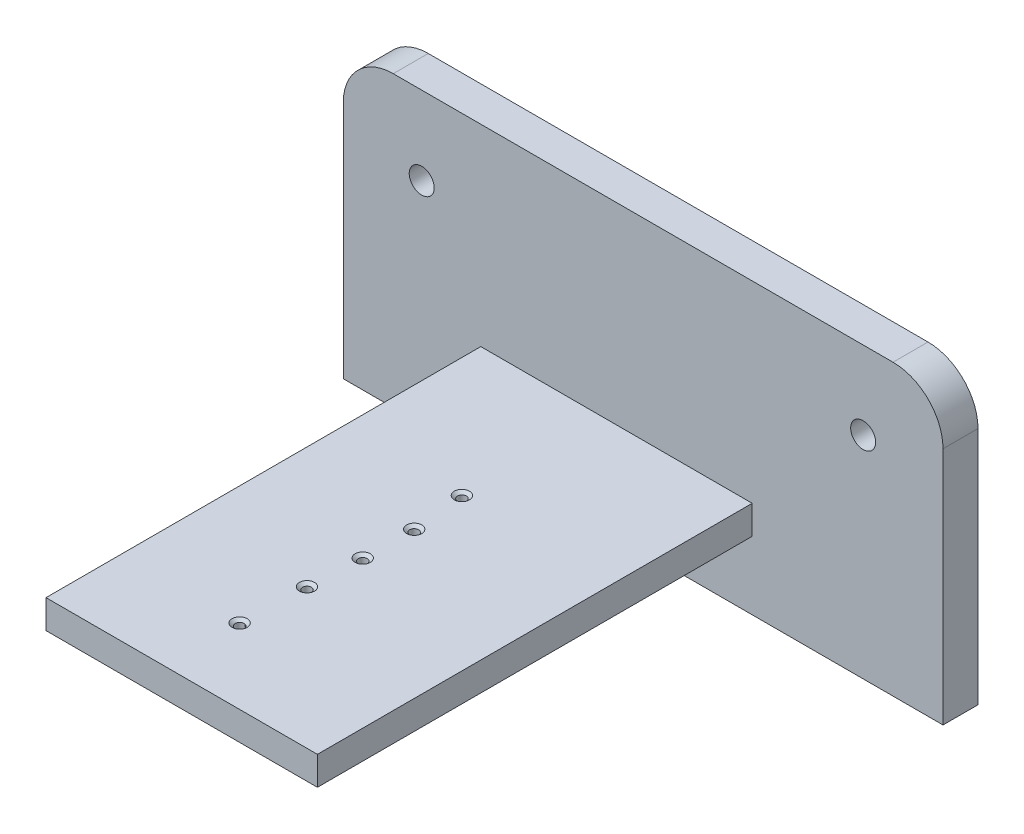
SolidWorks part; units mm, degrees
ref_plane "Front Plane" through (0, 0, 0) normal (0, 0, 1) x (1, 0, 0)
ref_plane "Top Plane" through (0, 0, 0) normal (0, 1, 0) x (1, 0, 0)
ref_plane "Right Plane" through (0, 0, 0) normal (1, 0, 0) x (0, 0, -1)
sketch "Sketch1" plane through (0, 0, 0) normal (0, 0, 1) x (1, 0, 0)
  line L1 (-60.1068, -28.7722) -> (59.8932, -28.7722)
  line L2 (-60.1068, -28.7722) -> (-60.1068, 29.0925)
  line L3 (-60.1068, 29.0925) -> (59.8932, 29.0925)
  line L4 (59.8932, -28.7722) -> (59.8932, 29.0925)
  line L5 (-60.1068, -28.7722) -> (59.8932, 29.0925) construction
  line L6 (-60.1068, 29.0925) -> (59.8932, -28.7722) construction
  line L7 (-60.2135, 13.6121) -> (59.573, 13.5053) construction
  circle A0 centre (-44.4128, 13.3986) radius 2.5
  circle A2 centre (43.913, 13.4684) radius 2.5
  point P0 (-0.1068, 0.1601)
  point P13 (0, 0)
  point P16 (42.4773, 12.7928)
  point P17 (40.5349, 13.7217)
  point P18 (43.913, 13.4684)
  dimension "D3" = 5
  dimension "D4" = 5
  dimension "D1" = 120
  dimension "D2" = 57.8648
extrude "Boss-Extrude1" add sketch "Sketch1" along normal blind 7
sketch "Sketch2" plane through (0, 0, 7) normal (0, 0, 1) x (1, 0, 0)
  line L1 (-32.5899, -15.1625) -> (21.7161, -15.1625)
  line L2 (-32.5899, -15.1625) -> (-32.5899, -9.4426)
  line L3 (-32.5899, -9.4426) -> (21.7161, -9.4426)
  line L4 (21.7161, -15.1625) -> (21.7161, -9.4426)
  line L5 (-32.5899, -15.1625) -> (21.7161, -9.4426) construction
  line L6 (-32.5899, -9.4426) -> (21.7161, -15.1625) construction
  point P0 (-5.4369, -12.3026)
extrude "Boss-Extrude2" add sketch "Sketch2" along normal blind 87
fillet "Fillet1" radius 10 2 edges at (59.8932, 29.0925, 3.5) (-60.1068, 29.0925, 3.5)
hole_wizard "CSK for #0 Flat Head Machine Screw (100)1" positions "Sketch3" profile "Sketch4" countersink size "#0" standard "ANSI Inch" end condition through all
sketch "Sketch3" plane through (0, -9.4426, 0) normal (0, 1, 0) x (1, 0, 0)
  point P0 (-8.6754, -34.6996)
  point P2 (-7.5993, -45.3149)
  point P4 (-7.7572, -55.463)
  point P6 (-8.364, -66.0078)
  point P8 (-8.8168, -79.0274)
sketch "Sketch4" plane through (-8.6754, -9.4426, 34.6996) normal (1, 0, 0) x (0, 0, 1)
  line L0 (0, 0) -> (0, 19.3296)
  line L1 (0, 19.3296) -> (0.889, 19.3296)
  line L2 (0.889, 19.3296) -> (0.889, 0.5222)
  line L3 (0.889, 0.5222) -> (1.5113, 0)
  line L5 (1.5113, 0) -> (0, 0)
  line L6 (-0.889, 0.5222) -> (-1.5113, 0) construction
  line L11 (0, -6.35) -> (0, 107.95) construction
  dimension "Thru Hole Dia." = 1.778
  dimension "Thru Hole Depth" = 19.3296
  dimension "Near C'Sink Dia." = 3.0226
  dimension "Near C'Sink Angle" = 100
